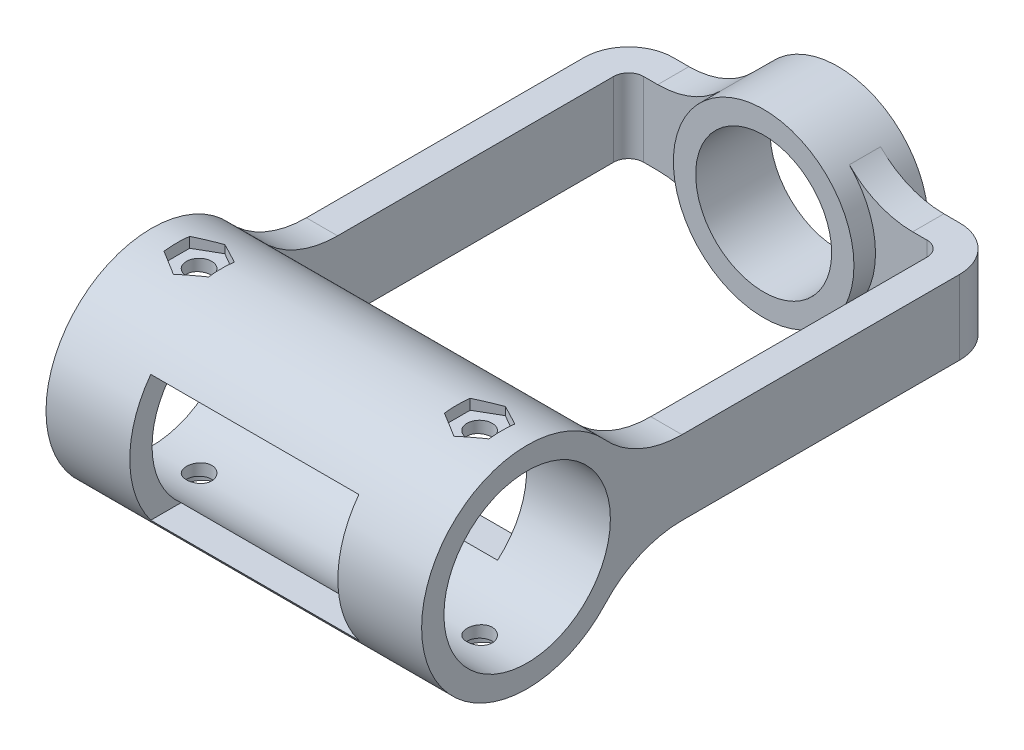
SolidWorks part; units mm, degrees
ref_plane "Front Plane" through (0, 0, 0) normal (0, 0, 1) x (1, 0, 0)
ref_plane "Top Plane" through (0, 0, 0) normal (0, 1, 0) x (1, 0, 0)
ref_plane "Right Plane" through (0, 0, 0) normal (1, 0, 0) x (0, 0, -1)
sketch "Sketch1" plane through (0, 0, 0) normal (0, 0, 1) x (1, 0, 0)
  circle A1 centre (0, 0) radius 9.15
  circle A2 centre (0, 0) radius 12.15
  dimension "D1" = 18.3
  dimension "D2" = 3
extrude "Boss-Extrude1" add sketch "Sketch1" along normal blind 10
ref_plane "Plane1" through (0, 0, 5) normal (0, 0, 1) x (1, 0, 0)
sketch "Sketch2" plane through (0, 0, 5) normal (0, 0, 1) x (1, 0, 0)
  line L0 (11.0735, 5) -> (21.0735, 5)
  line L1 (11.0735, -5) -> (21.0735, -5)
  line L2 (21.0735, 5) -> (21.0735, -5)
  line L3 (0, 3.551) -> (0, -3.551) construction
  line L4 (-21.0735, 5) -> (-21.0735, -5)
  line L5 (-11.0735, -5) -> (-21.0735, -5)
  line L6 (-11.0735, 5) -> (-21.0735, 5)
  circle A0 centre (0, 0) radius 12.15 construction
  arc A1 (11.0735, 5) -> (11.0735, -5) centre (0, 0) cw
  arc A2 (-11.0735, 5) -> (-11.0735, -5) centre (0, 0) ccw
  point P10 (0, 0)
  dimension "D1" = 5
  dimension "D2" = 5
  dimension "D3" = 10
extrude "Boss-Extrude2" add sketch "Sketch2" along normal blind 2.1 and the other way blind 2.1 contours L0 A1 L1 L2 | A2 L6 L4 L5
sketch "Sketch4" plane through (0, 0, 2.9) normal (0, 0, -1) x (-1, 0, 0)
  line L0 (11.0735, -5) -> (21.0735, -5) construction
  line L1 (21.0735, 5) -> (25.2735, 5)
  line L2 (21.0735, 5) -> (21.0735, -5)
  line L3 (21.0735, -5) -> (25.2735, -5)
  line L4 (25.2735, 5) -> (25.2735, -5)
  line L5 (0, 5.0014) -> (0, -5.0014) construction
  line L6 (-21.0735, 5) -> (-21.0735, -5)
  line L7 (-21.0735, -5) -> (-25.2735, -5)
  line L8 (-25.2735, 5) -> (-25.2735, -5)
  line L9 (-21.0735, 5) -> (-25.2735, 5)
  point P13 (0, 0)
  dimension "D1" = 4.2
extrude "Boss-Extrude3" add sketch "Sketch4" against normal blind 53
fillet "Fillet1" radius 12 4 edges at (11.0735, 5, 5) (11.0735, -5, 5) (-11.0735, -5, 5) (-11.0735, 5, 5)
sketch "Sketch5" plane through (-25.2735, 0, 0) normal (-1, 0, 0) x (0, 0, 1)
  line L0 (55.9, -5) -> (55.9, 5) construction
  circle A0 centre (67.1, 0) radius 11.2
  circle A1 centre (67.1, 0) radius 14.2
  point P5 (55.9, 0)
  dimension "D1" = 22.4
  dimension "D2" = 3
extrude "Boss-Extrude4" add sketch "Sketch5" against normal up to surface (50.547 mm away) separate body up to face at (25.2735, 0, 29.4)
sketch "Sketch7" plane through (-25.2735, 0, 0) normal (-1, 0, 0) x (0, 0, 1)
  line L0 (55.9, -5) -> (2.9, -5) construction
  line L4 (67.1, 0) -> (39.1577, 0) construction
  line L5 (56.6069, -9.5674) -> (56.6069, 9.5674)
  line L6 (46.2616, -5) -> (46.2616, 5)
  arc A0 (56.6069, -9.5674) -> (46.2616, -5) centre (46.2616, -19) ccw
  circle A1 centre (67.1, 0) radius 14.2 construction
  arc A2 (56.6069, 9.5674) -> (46.2616, 5) centre (46.2616, 19) cw
  dimension "D1" = 14
extrude "Boss-Extrude11" add sketch "Sketch7" against normal up to surface (4.2 mm away) up to face at (-21.0735, 0, 31.5)
sketch "Sketch8" plane through (0, 0, 0) normal (0, 1, 0) x (1, 0, 0)
  line L0 (25.2735, -81.3) -> (25.2735, -53.8094) construction
  line L1 (-15.2735, -75.3) -> (15.2735, -75.3)
  line L2 (-15.2735, -75.3) -> (-15.2735, -58.9)
  line L3 (-15.2735, -58.9) -> (15.2735, -58.9)
  line L4 (15.2735, -75.3) -> (15.2735, -58.9)
  line L5 (-25.2735, -56.6069) -> (-25.2735, -81.3) construction
  line L6 (-25.2735, -81.3) -> (25.2735, -81.3) construction
  line L7 (21.0735, -52.9) -> (-21.0735, -52.9) construction
  dimension "D1" = 10
  dimension "D2" = 10
  dimension "D3" = 6
  dimension "D4" = 6
extrude "Cut-Extrude1" [suppressed] cut sketch "Sketch8" against normal through all and the other way through all
sketch "Sketch9" plane through (25.2735, 0, 0) normal (1, 0, 0) x (0, 0, -1)
  line L2 (-56.6069, 9.5674) -> (-56.6069, -9.5674)
  line L3 (-46.2616, -5) -> (-46.2616, 5)
  line L4 (-56.6069, 9.5674) -> (-56.6069, -9.5674)
  line L5 (-46.2616, -5) -> (-46.2616, 5)
  arc A2 (-56.6069, 9.5674) -> (-46.2616, 5) centre (-46.2616, 19) ccw
  arc A3 (-46.2616, -5) -> (-56.6069, -9.5674) centre (-46.2616, -19) ccw
  arc A4 (-56.6069, 9.5674) -> (-46.2616, 5) centre (-46.2616, 19) ccw
  arc A5 (-46.2616, -5) -> (-56.6069, -9.5674) centre (-46.2616, -19) ccw
  dimension "D1" = 0
extrude "Boss-Extrude12" add sketch "Sketch9" against normal up to surface (4.2 mm away) up to face at (21.0735, 0, 30.2274)
fillet "Fillet2" radius 6 2 edges at (-25.2735, 0, 2.9) (25.2735, 0, 2.9)
fillet "Fillet3" radius 2 2 edges at (-21.0735, 0, 7.1) (21.0735, 0, 7.1)
sketch "Sketch10" plane through (25.2735, 0, 0) normal (1, 0, 0) x (0, 0, -1)
  circle A0 centre (-67.1, 0) radius 11.2
  arc A1 (-56.6069, 3.916) -> (-56.6069, -3.916) centre (-67.1, 0) ccw construction
extrude "Cut-Extrude2" cut sketch "Sketch10" against normal through all
ref_plane "Plane3" through (0, -14.2, 0) normal (0, -1, 0) x (-1, 0, 0)
sketch "Sketch15" plane through (0, -14.2, 0) normal (0, -1, 0) x (-1, 0, 0)
  line L0 (-25.2735, -55.9) -> (-25.2735, -78.3) construction
  line L1 (-25.2735, -56.6069) -> (-25.2735, -81.3) construction
  line L2 (25.2735, -81.3) -> (25.2735, -56.6069) construction
  circle A0 centre (-18.8735, -67.1) radius 1.7
  circle A1 centre (18.8735, -67.1) radius 1.7
  point P4 (0, 0)
  point P7 (-25.2735, -67.1)
  point P10 (0, 0)
  dimension "D1" = 3.4
  dimension "D2" = 6.4
  dimension "D3" = 6.4
extrude "Cut-Extrude5" cut sketch "Sketch15" against normal through all and the other way through all
ref_plane "Plane4" through (0, -14.2, 0) normal (0, -1, 0) x (-1, 0, 0)
sketch "Sketch17" plane through (0, -14.2, 0) normal (0, -1, 0) x (-1, 0, 0)
  line L0 (0, -81.3) -> (0, -52.9) construction
  line L1 (-25.2735, -81.3) -> (25.2735, -81.3) construction
  line L2 (21.0735, -52.9) -> (-21.0735, -52.9) construction
  circle A0 centre (-18.8735, -67.1) radius 2.9
  circle A1 centre (18.8735, -67.1) radius 2.9
  dimension "D1" = 5.8
extrude "Cut-Extrude6" cut sketch "Sketch17" against normal blind 1.5
ref_plane "Plane5" through (0, 14.2, 0) normal (0, 1, 0) x (1, 0, 0)
sketch "Sketch18" plane through (0, 14.2, 0) normal (0, 1, 0) x (1, 0, 0)
  line L0 (-25.2735, -56.6069) -> (-25.2735, -81.3) construction
  line L1 (-15.8735, -68.8321) -> (-15.8735, -65.3679)
  line L2 (-15.8735, -65.3679) -> (-18.8735, -63.6359)
  line L3 (-18.8735, -63.6359) -> (-21.8735, -65.3679)
  line L4 (-21.8735, -65.3679) -> (-21.8735, -68.8321)
  line L5 (-21.8735, -68.8321) -> (-18.8735, -70.5641)
  line L6 (-18.8735, -70.5641) -> (-15.8735, -68.8321)
  line L7 (21.8735, -68.8321) -> (21.8735, -65.3679)
  line L8 (21.8735, -65.3679) -> (18.8735, -63.6359)
  line L9 (18.8735, -63.6359) -> (15.8735, -65.3679)
  line L10 (15.8735, -65.3679) -> (15.8735, -68.8321)
  line L11 (15.8735, -68.8321) -> (18.8735, -70.5641)
  line L12 (18.8735, -70.5641) -> (21.8735, -68.8321)
  circle A0 centre (-18.8735, -67.1) radius 3 construction
  circle A1 centre (18.8735, -67.1) radius 3 construction
  dimension "D1" = 6
extrude "Cut-Extrude7" cut sketch "Sketch18" against normal blind 1.5
ref_plane "Plane6" through (0, 0, 55.9) normal (0, 0, 1) x (1, 0, 0)
sketch "Sketch19" plane through (0, 0, 55.9) normal (0, 0, 1) x (1, 0, 0)
  line L1 (14, -8.5) -> (-14, -8.5)
  line L2 (14, -8.5) -> (14, 8.5)
  line L3 (14, 8.5) -> (-14, 8.5)
  line L4 (-14, -8.5) -> (-14, 8.5)
  point P4 (14, 0)
  point P7 (0, 8.5)
  dimension "D1" = 28
  dimension "D2" = 17
extrude "Cut-Extrude8" cut sketch "Sketch19" against normal blind 4 and the other way through all
